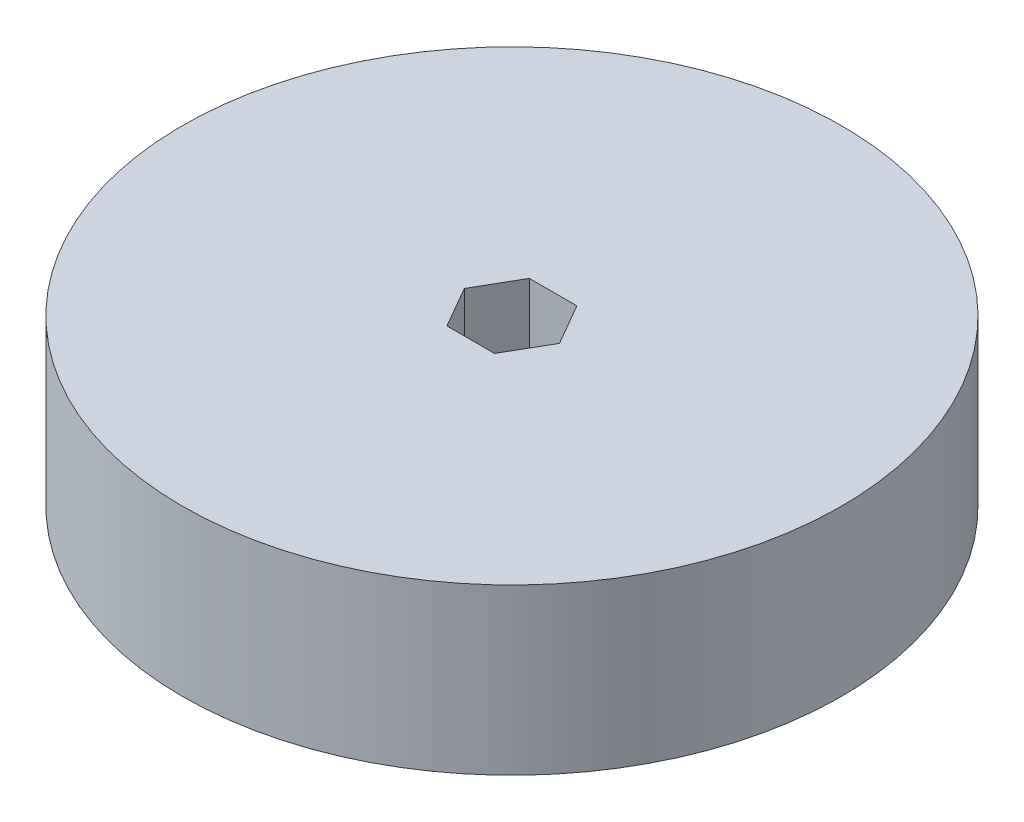
SolidWorks part; units mm, degrees
ref_plane "Front Plane" through (0, 0, 0) normal (0, 0, 1) x (1, 0, 0)
ref_plane "Top Plane" through (0, 0, 0) normal (0, 1, 0) x (1, 0, 0)
ref_plane "Right Plane" through (0, 0, 0) normal (1, 0, 0) x (0, 0, -1)
sketch "Sketch1" plane through (0, 0, 0) normal (0, 1, 0) x (1, 0, 0)
  line L1 (7.3323, 0) -> (3.6662, 6.35)
  line L2 (3.6662, 6.35) -> (-3.6662, 6.35)
  line L3 (-3.6662, 6.35) -> (-7.3323, 0)
  line L4 (-7.3323, 0) -> (-3.6662, -6.35)
  line L5 (-3.6662, -6.35) -> (3.6662, -6.35)
  line L6 (3.6662, -6.35) -> (7.3323, 0)
  circle A0 centre (0, 0) radius 6.35 construction
  circle A1 centre (0, 0) radius 50.8
  dimension "D1" = 12.7
  dimension "D2" = 101.6
extrude "Boss-Extrude1" add sketch "Sketch1" along normal blind 25.4
